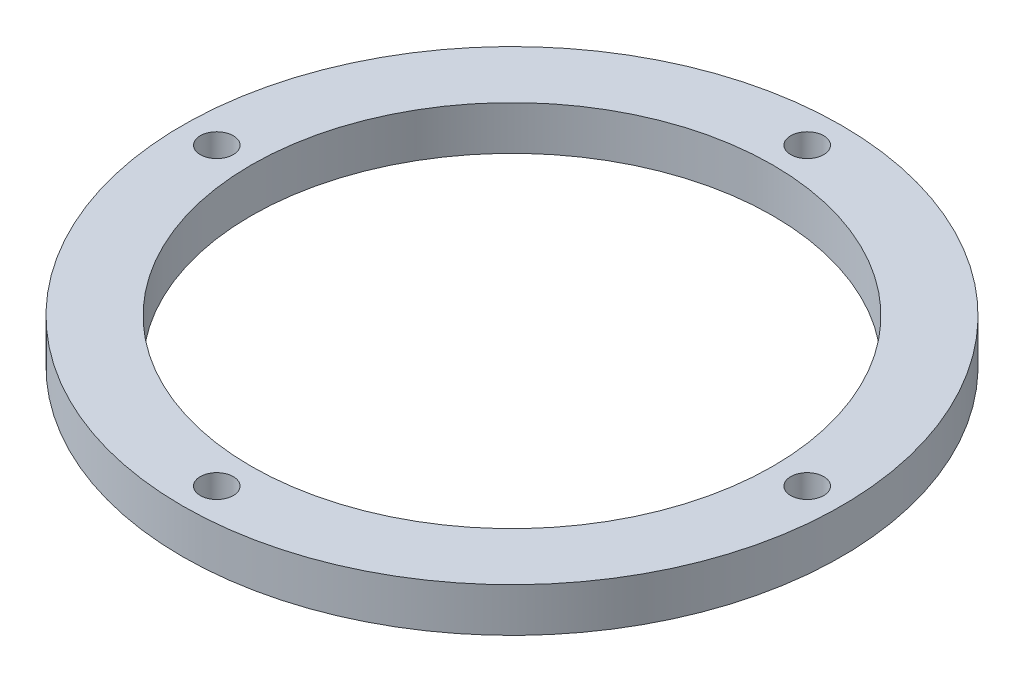
SolidWorks part; units mm, degrees
ref_plane "前视基准面" through (0, 0, 0) normal (0, 0, 1) x (1, 0, 0)
ref_plane "上视基准面" through (0, 0, 0) normal (0, 1, 0) x (1, 0, 0)
ref_plane "右视基准面" through (0, 0, 0) normal (1, 0, 0) x (0, 0, -1)
other "Configuration Table"
sketch "草图1" plane through (0, 0, 0) normal (0, 1, 0) x (1, 0, 0)
  line L1 (47.5, 0) -> (60, 0)
  circle A0 centre (0, 0) radius 60
  circle A2 centre (0, 0) radius 47.5
  circle A3 centre (53.75, 0) radius 3
  circle A4 centre (0, -53.75) radius 3
  circle A5 centre (-53.75, 0) radius 3
  circle A6 centre (0, 53.75) radius 3
  point P17 (0, 0)
  dimension "D1" = 95
  dimension "D2" = 120
  dimension "D3" = 4
extrude "凸台-拉伸1" add sketch "草图1" along normal blind 8
